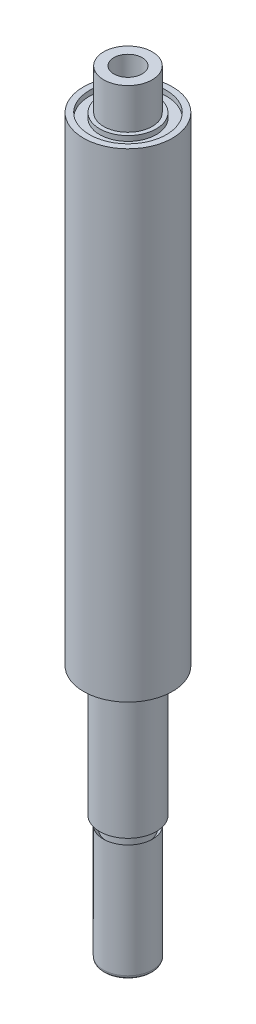
SolidWorks part; units mm, degrees
ref_plane "Alzado" through (0, 0, 0) normal (0, 0, 1) x (1, 0, 0)
ref_plane "Planta" through (0, 0, 0) normal (0, 1, 0) x (1, 0, 0)
ref_plane "Vista lateral" through (0, 0, 0) normal (1, 0, 0) x (0, 0, -1)
sketch "Croquis1" plane through (0, 0, 0) normal (0, 0, 1) x (1, 0, 0)
  line L0 (0, 29.4848) -> (0, -145.2172) construction
  line L1 (3.5, 46.2828) -> (6, 46.2828)
  line L2 (6, 46.2828) -> (6, 36.2828)
  line L3 (6, 36.2828) -> (7, 36.2828)
  line L4 (7, 36.2828) -> (7, 35.0328)
  line L5 (7, 35.0328) -> (9.5, 35.0328)
  line L6 (9.5, 35.0328) -> (9.5, 36.2828)
  line L7 (9.5, 36.2828) -> (11, 36.2828)
  line L8 (11, 36.2828) -> (11, -82.2172)
  line L9 (11, -82.2172) -> (7, -82.2172)
  line L10 (7, -82.2172) -> (7, -114.2172)
  line L11 (7, -114.2172) -> (5.1616, -114.2172)
  line L12 (5.1616, -114.2172) -> (5.1616, -117.2172)
  line L13 (5.1616, -117.2172) -> (6.0808, -116.298)
  line L14 (6.0808, -116.298) -> (6.0808, -144.298)
  line L15 (5.1616, -145.2172) -> (0, -145.2172)
  line L16 (0, -145.2172) -> (0, 21.2828)
  line L17 (0, 21.2828) -> (3.5, 21.2828)
  line L18 (3.5, 21.2828) -> (3.5, 46.2828)
  arc A0 (6.0808, -144.298) -> (5.1616, -145.2172) centre (5.1616, -144.298) cw
  dimension "D1" = 3.5
  dimension "D2" = 25
  dimension "D3" = 6
  dimension "D4" = 10
  dimension "D5" = 7
  dimension "D6" = 2.5
  dimension "D7" = 1.25
  dimension "D8" = 11
  dimension "D9" = 118.5
  dimension "D10" = 32
  dimension "191.5" = 191.5
  dimension "D11" = 3
  dimension "D12" = 28
revolve "Revolución1" add sketch "Croquis1" angle 360 about L0
